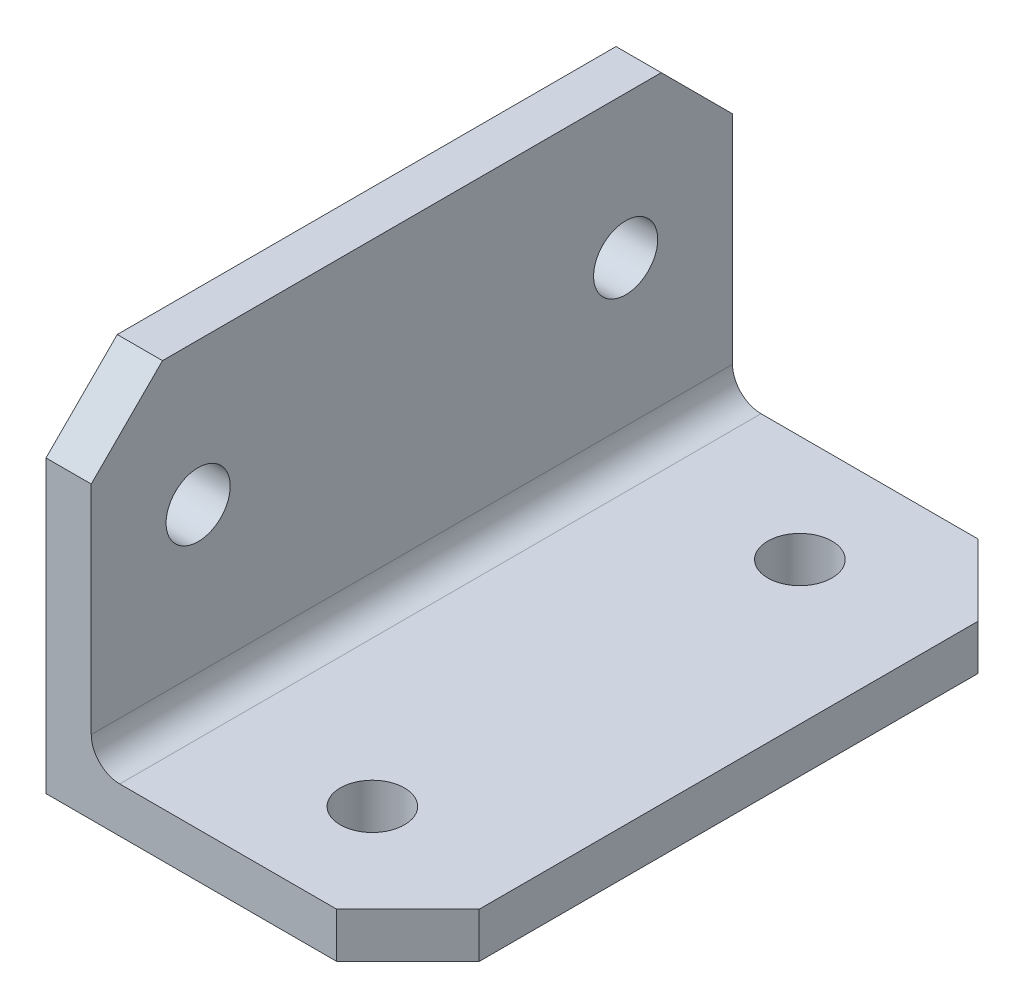
SolidWorks part; units mm, degrees
material "6061-T6 (SS)"
ref_plane "Front Plane" through (0, 0, 0) normal (0, 0, 1) x (1, 0, 0)
ref_plane "Top Plane" through (0, 0, 0) normal (0, 1, 0) x (1, 0, 0)
ref_plane "Right Plane" through (0, 0, 0) normal (1, 0, 0) x (0, 0, -1)
sketch "Sketch1" plane through (0, 0, 0) normal (0, 0, 1) x (1, 0, 0)
  line L0 (0, 0) -> (0, 25.4)
  line L1 (0, 25.4) -> (3.175, 25.4)
  line L2 (3.175, 25.4) -> (3.175, 3.175)
  line L3 (3.175, 3.175) -> (25.4, 3.175)
  line L4 (25.4, 3.175) -> (25.4, 0)
  line L5 (25.4, 0) -> (0, 0)
  dimension "D1" = 25.4
  dimension "D2" = 3.175
extrude "Boss-Extrude1" add sketch "Sketch1" along normal mid plane 45
sketch "Sketch4" plane through (0, 3.175, 0) normal (0, 1, 0) x (1, 0, 0)
  line L0 (25.4, -22.5) -> (25.4, 22.5) construction
  point P0 (15.4, 15)
  point P2 (15.4, -15)
  point P5 (0, 0)
  dimension "D1" = 10
  dimension "D2" = 15
  dimension "D3" = 15
hole_wizard "M4 Clearance Hole1" positions "Sketch4" profile "Sketch3" hole size "M4" standard "ANSI Metric" end condition through all
sketch "Sketch3" plane through (15.4, 3.175, -15) normal (1, 0, 0) x (0, 0, 1)
  line L0 (0, 0) -> (0, 3.175)
  line L1 (0, 3.175) -> (2.25, 3.175)
  line L2 (2.25, 3.175) -> (2.25, 0)
  line L5 (2.25, 0) -> (0, 0)
  line L11 (0, -6.35) -> (0, 107.95) construction
  dimension "Thru Hole Dia." = 4.5
  dimension "Thru Hole Depth" = 3.175
sketch "Sketch7" plane through (3.175, 0, 0) normal (1, 0, 0) x (0, 0, -1)
  line L0 (-22.5, 25.4) -> (22.5, 25.4) construction
  point P0 (-15, 15.4)
  point P2 (15, 15.4)
  point P8 (0, 0)
  dimension "D1" = 10
  dimension "D2" = 15
  dimension "D3" = 15
hole_wizard "M4 Clearance Hole2" positions "Sketch7" profile "Sketch6" hole size "M4" standard "ANSI Metric" end condition through all
sketch "Sketch6" plane through (3.175, 15.4, 15) normal (0, 1, 0) x (0, 0, -1)
  line L0 (0, 0) -> (0, 3.175)
  line L1 (0, 3.175) -> (2.25, 3.175)
  line L2 (2.25, 3.175) -> (2.25, 0)
  line L5 (2.25, 0) -> (0, 0)
  line L11 (0, -6.35) -> (0, 107.95) construction
  dimension "Thru Hole Dia." = 4.5
  dimension "Thru Hole Depth" = 3.175
fillet "Fillet1" radius 2 1 edges at (3.175, 3.175, 0)
chamfer "Chamfer1" distance 5 angle 45 4 edges at (25.4, 1.5875, 22.5) (25.4, 1.5875, -22.5) (1.5875, 25.4, -22.5) (1.5875, 25.4, 22.5)
